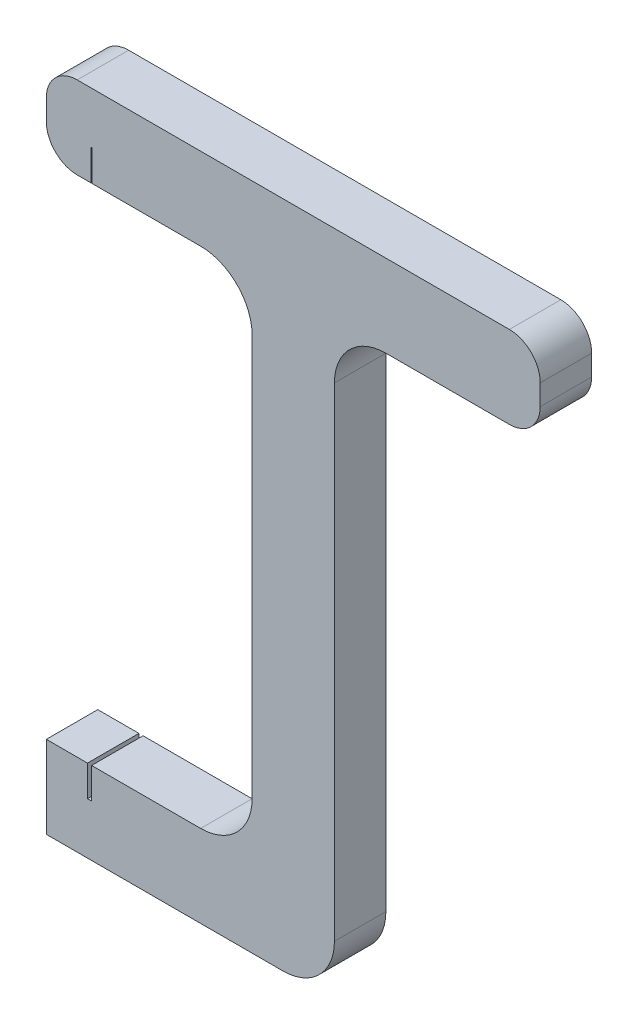
SolidWorks part; units mm, degrees
ref_plane "Front Plane" through (0, 0, 0) normal (0, 0, 1) x (1, 0, 0)
ref_plane "Top Plane" through (0, 0, 0) normal (0, 1, 0) x (1, 0, 0)
ref_plane "Right Plane" through (0, 0, 0) normal (1, 0, 0) x (0, 0, -1)
sketch "Sketch1" plane through (0, 0, 0) normal (0, 0, 1) x (1, 0, 0)
  line L1 (0, 65) -> (-28, 65)
  line L2 (-28, 65) -> (-28, 57)
  line L3 (-28, 57) -> (-8, 57)
  line L4 (-8, 57) -> (-8, 8)
  line L5 (-8, 8) -> (-28, 8)
  line L6 (-28, 8) -> (-28, 0)
  line L7 (-28, 0) -> (0, 0)
  line L11 (0, 0) -> (0, 57)
  line L12 (0, 57) -> (20, 57)
  line L13 (20, 57) -> (20, 65)
  line L14 (20, 65) -> (0, 65)
  dimension "D3" = 8
  dimension "D4" = 20
  dimension "D5" = 20
  dimension "D6" = 65
  dimension "D1" = 20
  dimension "D2" = 8
  dimension "D7" = 8
  dimension "D8" = 20
extrude "Boss-Extrude1" add sketch "Sketch1" along normal blind 5
sketch "Sketch2" plane through (0, 8, 0) normal (0, 1, 0) x (1, 0, 0)
  line L0 (0, 0) -> (-23.8, 0) construction
  line L1 (-8, 0) -> (-28, 0) construction
  line L2 (-23.8, 0) -> (-23.8, -5) construction
  line L3 (-8, -5) -> (-28, -5) construction
  line L5 (-24, -5) -> (-23.6, -5)
  line L6 (-24, -5) -> (-24, 0)
  line L7 (-24, 0) -> (-23.6, 0)
  line L8 (-23.6, -5) -> (-23.6, 0)
  line L9 (-24, -5) -> (-23.6, 0) construction
  line L10 (-24, 0) -> (-23.6, -5) construction
  point P5 (-23.8, -2.5)
  dimension "D1" = 23.8
  dimension "D2" = 0.4
extrude "Cut-Extrude1" cut sketch "Sketch2" against normal blind 3
sketch "Sketch3" plane through (0, 57, 0) normal (0, -1, 0) x (1, 0, 0)
  line L0 (-23.65, 2.5) -> (0, 2.5) construction
  line L3 (-23.65, 5) -> (-23.55, 5)
  line L4 (-23.65, 5) -> (-23.65, 0)
  line L5 (-23.65, 0) -> (-23.55, 0)
  line L6 (-23.55, 5) -> (-23.55, 0)
  line L7 (-23.65, 5) -> (-23.55, 0) construction
  line L8 (-23.65, 0) -> (-23.55, 5) construction
  line L9 (0, 5) -> (0, 0) construction
  dimension "D2" = 0.1
  dimension "D1" = 23.65
extrude "Cut-Extrude2" cut sketch "Sketch3" against normal blind 3
fillet "Fillet1" radius 5 4 edges at (0, 57, 2.5) (-8, 57, 2.5) (0, 0, 2.5) (-8, 8, 2.5)
fillet "Fillet2" radius 3 4 edges at (-28, 57, 2.5) (20, 57, 2.5) (20, 65, 2.5) (-28, 65, 2.5)
equation "\"A.L\"= 0.07m"
equation "\"A.h\"= 0.007m"
equation "\"A.d\"= 0.005m"
equation "\"A.delta\"= 45.0001"
equation "\"A.w\"= 0m"
equation "\"A.v\"= 0.013m"
equation "\"A.s\"= 0.014m"
equation "\"A.t\"= 0.007m"
equation "\"B.L\"= 0.065m"
equation "\"B.h\"= 0.008m"
equation "\"B.s\"= 0.016m"
equation "\"B.t\"= 0.008m"
equation "\"C.h\"= 0.0065m"
equation "\"C.d\"= 0.005m"
equation "\"C.L\"= 0.05m"
equation "\"C.wmax\"= 0.003m"
equation "\"D.L\"= 0.06m"
equation "\"D.h\"= 0.008m"
equation "\"D.s\"= 0.012m"
equation "\"D.t\"= 0.008m"
equation "\"a_h\"= 0.0001m"
equation "\"a_d\"= 0.005m"
equation "\"a_L\"= 0.008m"
equation "\"b_h\"= 0.0004m"
equation "\"b_d\"= 0.005m"
equation "\"b_L\"= 0.007m"
equation "\"c_h\"= 0.0001m"
equation "\"c_d\"= 0.005m"
equation "\"c_L\"= 0.01m"
equation "\"d_h\"= 0.0001m"
equation "\"d_d\"= 0.005m"
equation "\"d_L\"= 0.01m"
equation "\"S.h\"= 0.015m"
equation "\"S.L\"= 0.09275m"
equation "\"D3@Sketch1\"=\"B.t\""
equation "\"D4@Sketch1\"=\"B.s\"+4"
equation "\"D5@Sketch1\"=\"B.s\"+4"
equation "\"D6@Sketch1\"=\"B.L\""
equation "\"D1@Sketch2\"=\"B.h\"+\"B.s\"-\"b_h\"/2"
equation "\"D2@Sketch2\"=\"b_h\""
equation "\"D2@Sketch3\"=\"c_h\""
equation "\"D2@Sketch1\"=\"B.t\""
equation "\"D7@Sketch1\"=\"B.h\""
equation "\"D1@Sketch3\"=\"B.h\"+\"B.s\"-\"c_h\"/2-0.3"
